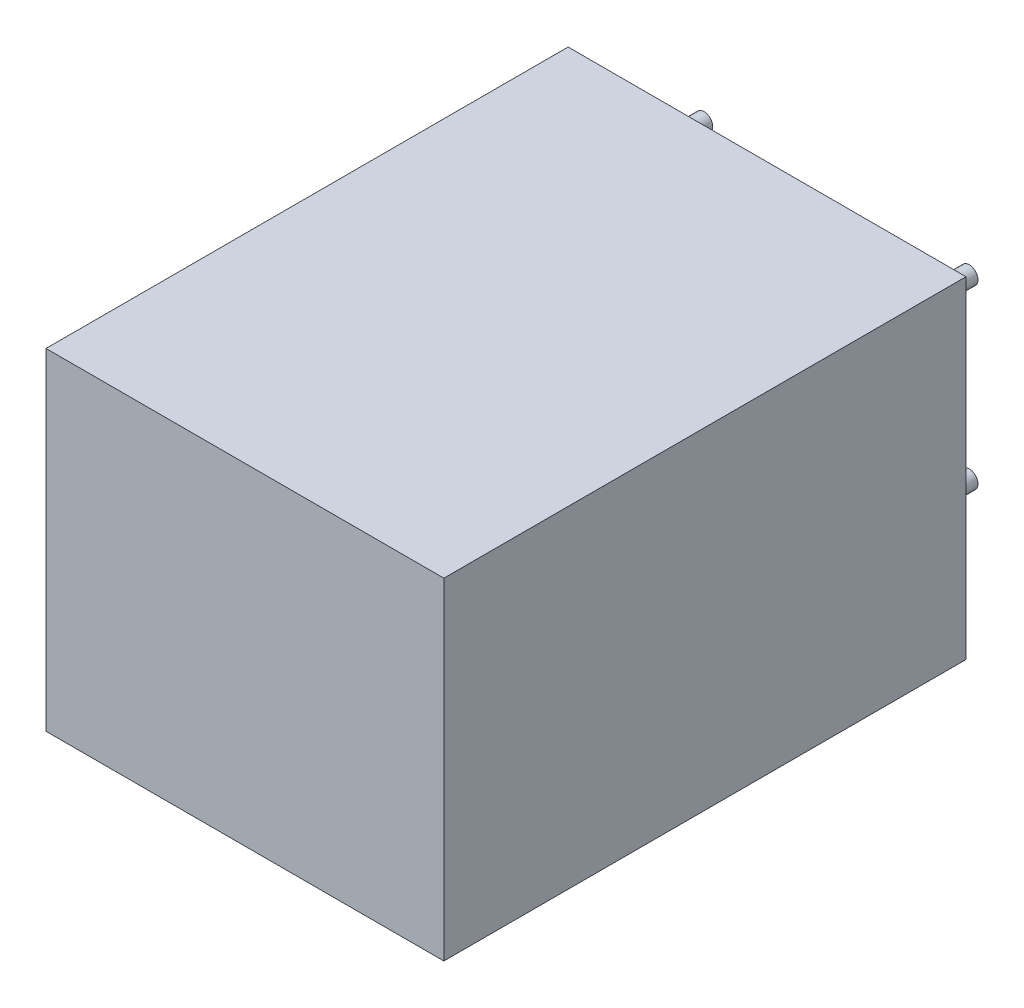
SolidWorks part; units mm, degrees
ref_plane "Front Plane" through (0, 0, 0) normal (0, 0, 1) x (1, 0, 0)
ref_plane "Top Plane" through (0, 0, 0) normal (0, 1, 0) x (1, 0, 0)
ref_plane "Right Plane" through (0, 0, 0) normal (1, 0, 0) x (0, 0, -1)
sketch "Sketch1" plane through (0, 0, 0) normal (0, 0, 1) x (1, 0, 0)
  line L0 (-1.905, 6.985) -> (-1.905, -2.54)
  line L1 (-1.905, -2.54) -> (9.525, -2.54)
  line L2 (9.525, -2.54) -> (9.525, 6.985)
  line L3 (9.525, 6.985) -> (-1.905, 6.985)
extrude "Component_Outline" add sketch "Sketch1" along normal blind 15 separate body
sketch "Sketch2" plane through (0, 0, 0) normal (0, 0, 1) x (1, 0, 0)
  circle A0 centre (0, 0) radius 0.25
extrude "1" add sketch "Sketch2" against normal blind 2 separate body
sketch "Sketch3" plane through (0, 0, 0) normal (0, 0, 1) x (1, 0, 0)
  circle A0 centre (0, 5.08) radius 0.25
extrude "2" add sketch "Sketch3" against normal blind 2 separate body
sketch "Sketch4" plane through (0, 0, 0) normal (0, 0, 1) x (1, 0, 0)
  circle A0 centre (7.62, 5.08) radius 0.25
extrude "3" add sketch "Sketch4" against normal blind 2 separate body
sketch "Sketch5" plane through (0, 0, 0) normal (0, 0, 1) x (1, 0, 0)
  circle A0 centre (7.62, 0) radius 0.25
extrude "4" add sketch "Sketch5" against normal blind 2 separate body
sketch3d "3DSketch1"
  line L0 (0, 0, 0) -> (1, 0, 0)
  line L1 (0, 0, 0) -> (0, 1, 0)
  line L2 (0, 0, 0) -> (0, 0, 1)
  point P0 (0, 0, 0)
